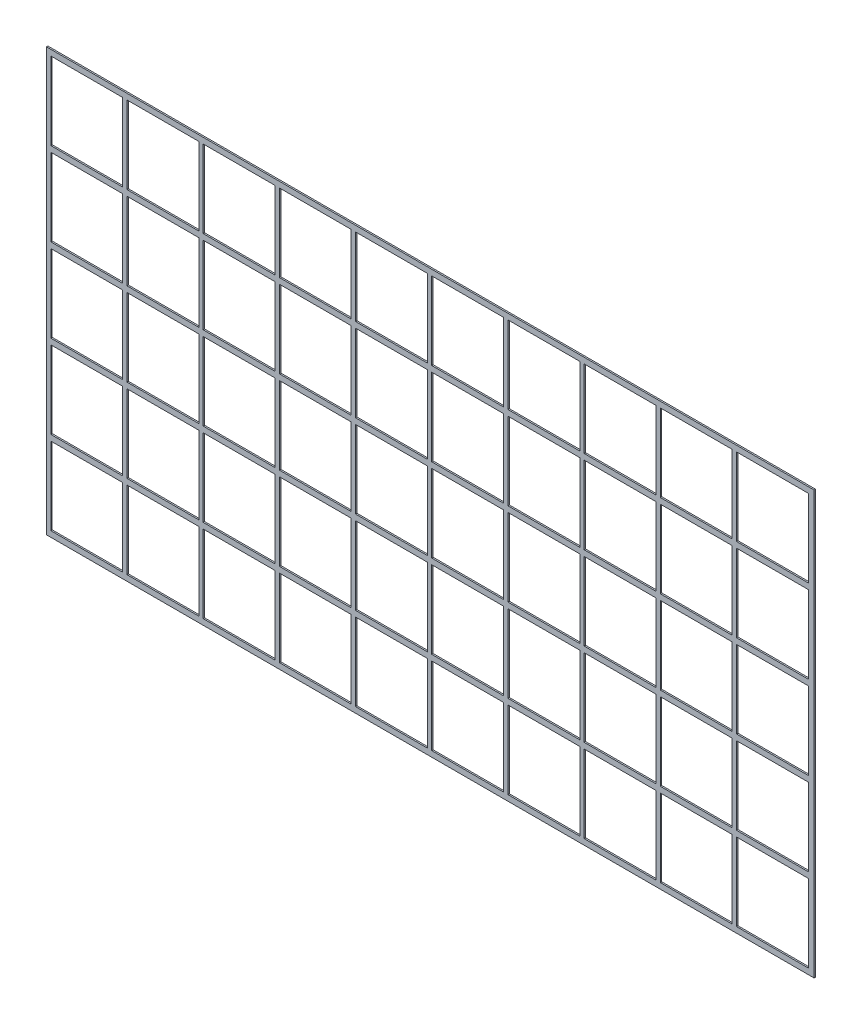
SolidWorks part; units mm, degrees
ref_plane "Front Plane" through (0, 0, 0) normal (0, 0, 1) x (1, 0, 0)
ref_plane "Top Plane" through (0, 0, 0) normal (0, 1, 0) x (1, 0, 0)
ref_plane "Right Plane" through (0, 0, 0) normal (1, 0, 0) x (0, 0, -1)
sketch "Sketch1" plane through (0, 0, 0) normal (0, 0, 1) x (1, 0, 0)
  line L1 (-847.725, -466.725) -> (847.725, -466.725)
  line L2 (-847.725, -466.725) -> (-847.725, 466.725)
  line L3 (-847.725, 466.725) -> (847.725, 466.725)
  line L4 (847.725, -466.725) -> (847.725, 466.725)
  line L5 (-847.725, -466.725) -> (847.725, 466.725) construction
  line L6 (-847.725, 466.725) -> (847.725, -466.725) construction
  point P0 (0, 0)
  dimension "D1" = 1695.45
  dimension "D2" = 933.45
extrude "Boss-Extrude1" add sketch "Sketch1" along normal blind 3.175
sketch "Sketch2" plane through (0, 0, 3.175) normal (0, 0, 1) x (1, 0, 0)
  line L1 (-679.45, 282.575) -> (-838.2, 282.575)
  line L2 (-679.45, 282.575) -> (-679.45, 454.025)
  line L3 (-679.45, 454.025) -> (-838.2, 454.025)
  line L4 (-838.2, 282.575) -> (-838.2, 454.025)
  line L5 (-679.45, 282.575) -> (-838.2, 454.025) construction
  line L6 (-679.45, 454.025) -> (-838.2, 282.575) construction
  line L8 (-511.175, 282.575) -> (-669.925, 282.575)
  line L9 (-511.175, 282.575) -> (-511.175, 454.025)
  line L10 (-511.175, 454.025) -> (-669.925, 454.025)
  line L11 (-669.925, 282.575) -> (-669.925, 454.025)
  line L12 (-342.9, 282.575) -> (-501.65, 282.575)
  line L13 (-342.9, 282.575) -> (-342.9, 454.025)
  line L14 (-342.9, 454.025) -> (-501.65, 454.025)
  line L15 (-501.65, 282.575) -> (-501.65, 454.025)
  line L16 (-174.625, 282.575) -> (-333.375, 282.575)
  line L17 (-174.625, 282.575) -> (-174.625, 454.025)
  line L18 (-174.625, 454.025) -> (-333.375, 454.025)
  line L19 (-333.375, 282.575) -> (-333.375, 454.025)
  line L20 (-6.35, 282.575) -> (-165.1, 282.575)
  line L21 (-6.35, 282.575) -> (-6.35, 454.025)
  line L22 (-6.35, 454.025) -> (-165.1, 454.025)
  line L23 (-165.1, 282.575) -> (-165.1, 454.025)
  line L24 (161.925, 282.575) -> (3.175, 282.575)
  line L25 (161.925, 282.575) -> (161.925, 454.025)
  line L26 (161.925, 454.025) -> (3.175, 454.025)
  line L27 (3.175, 282.575) -> (3.175, 454.025)
  line L28 (330.2, 282.575) -> (171.45, 282.575)
  line L29 (330.2, 282.575) -> (330.2, 454.025)
  line L30 (330.2, 454.025) -> (171.45, 454.025)
  line L31 (171.45, 282.575) -> (171.45, 454.025)
  line L32 (498.475, 282.575) -> (339.725, 282.575)
  line L33 (498.475, 282.575) -> (498.475, 454.025)
  line L34 (498.475, 454.025) -> (339.725, 454.025)
  line L35 (339.725, 282.575) -> (339.725, 454.025)
  line L36 (666.75, 282.575) -> (508, 282.575)
  line L37 (666.75, 282.575) -> (666.75, 454.025)
  line L38 (666.75, 454.025) -> (508, 454.025)
  line L39 (508, 282.575) -> (508, 454.025)
  line L40 (835.025, 282.575) -> (676.275, 282.575)
  line L41 (835.025, 282.575) -> (835.025, 454.025)
  line L42 (835.025, 454.025) -> (676.275, 454.025)
  line L43 (676.275, 282.575) -> (676.275, 454.025)
  line L44 (-511.175, 98.425) -> (-669.925, 98.425)
  line L45 (-511.175, 98.425) -> (-511.175, 269.875)
  line L46 (-511.175, 269.875) -> (-669.925, 269.875)
  line L47 (-669.925, 98.425) -> (-669.925, 269.875)
  line L48 (-342.9, 98.425) -> (-501.65, 98.425)
  line L49 (-342.9, 98.425) -> (-342.9, 269.875)
  line L50 (-342.9, 269.875) -> (-501.65, 269.875)
  line L51 (-501.65, 98.425) -> (-501.65, 269.875)
  line L52 (-174.625, 98.425) -> (-333.375, 98.425)
  line L53 (-174.625, 98.425) -> (-174.625, 269.875)
  line L54 (-174.625, 269.875) -> (-333.375, 269.875)
  line L55 (-333.375, 98.425) -> (-333.375, 269.875)
  line L56 (-6.35, 98.425) -> (-165.1, 98.425)
  line L57 (-6.35, 98.425) -> (-6.35, 269.875)
  line L58 (-6.35, 269.875) -> (-165.1, 269.875)
  line L59 (-165.1, 98.425) -> (-165.1, 269.875)
  line L60 (161.925, 98.425) -> (3.175, 98.425)
  line L61 (161.925, 98.425) -> (161.925, 269.875)
  line L62 (161.925, 269.875) -> (3.175, 269.875)
  line L63 (3.175, 98.425) -> (3.175, 269.875)
  line L64 (330.2, 98.425) -> (171.45, 98.425)
  line L65 (330.2, 98.425) -> (330.2, 269.875)
  line L66 (330.2, 269.875) -> (171.45, 269.875)
  line L67 (171.45, 98.425) -> (171.45, 269.875)
  line L68 (498.475, 98.425) -> (339.725, 98.425)
  line L69 (498.475, 98.425) -> (498.475, 269.875)
  line L70 (498.475, 269.875) -> (339.725, 269.875)
  line L71 (339.725, 98.425) -> (339.725, 269.875)
  line L72 (666.75, 98.425) -> (508, 98.425)
  line L73 (666.75, 98.425) -> (666.75, 269.875)
  line L74 (666.75, 269.875) -> (508, 269.875)
  line L75 (508, 98.425) -> (508, 269.875)
  line L76 (835.025, 98.425) -> (676.275, 98.425)
  line L77 (835.025, 98.425) -> (835.025, 269.875)
  line L78 (835.025, 269.875) -> (676.275, 269.875)
  line L79 (676.275, 98.425) -> (676.275, 269.875)
  line L80 (-511.175, -85.725) -> (-669.925, -85.725)
  line L81 (-511.175, -85.725) -> (-511.175, 85.725)
  line L82 (-511.175, 85.725) -> (-669.925, 85.725)
  line L83 (-669.925, -85.725) -> (-669.925, 85.725)
  line L84 (-342.9, -85.725) -> (-501.65, -85.725)
  line L85 (-342.9, -85.725) -> (-342.9, 85.725)
  line L86 (-342.9, 85.725) -> (-501.65, 85.725)
  line L87 (-501.65, -85.725) -> (-501.65, 85.725)
  line L88 (-174.625, -85.725) -> (-333.375, -85.725)
  line L89 (-174.625, -85.725) -> (-174.625, 85.725)
  line L90 (-174.625, 85.725) -> (-333.375, 85.725)
  line L91 (-333.375, -85.725) -> (-333.375, 85.725)
  line L92 (-6.35, -85.725) -> (-165.1, -85.725)
  line L93 (-6.35, -85.725) -> (-6.35, 85.725)
  line L94 (-6.35, 85.725) -> (-165.1, 85.725)
  line L95 (-165.1, -85.725) -> (-165.1, 85.725)
  line L96 (161.925, -85.725) -> (3.175, -85.725)
  line L97 (161.925, -85.725) -> (161.925, 85.725)
  line L98 (161.925, 85.725) -> (3.175, 85.725)
  line L99 (3.175, -85.725) -> (3.175, 85.725)
  line L100 (330.2, -85.725) -> (171.45, -85.725)
  line L101 (330.2, -85.725) -> (330.2, 85.725)
  line L102 (330.2, 85.725) -> (171.45, 85.725)
  line L103 (171.45, -85.725) -> (171.45, 85.725)
  line L104 (498.475, -85.725) -> (339.725, -85.725)
  line L105 (498.475, -85.725) -> (498.475, 85.725)
  line L106 (498.475, 85.725) -> (339.725, 85.725)
  line L107 (339.725, -85.725) -> (339.725, 85.725)
  line L108 (666.75, -85.725) -> (508, -85.725)
  line L109 (666.75, -85.725) -> (666.75, 85.725)
  line L110 (666.75, 85.725) -> (508, 85.725)
  line L111 (508, -85.725) -> (508, 85.725)
  line L112 (835.025, -85.725) -> (676.275, -85.725)
  line L113 (835.025, -85.725) -> (835.025, 85.725)
  line L114 (835.025, 85.725) -> (676.275, 85.725)
  line L115 (676.275, -85.725) -> (676.275, 85.725)
  line L116 (-511.175, -269.875) -> (-669.925, -269.875)
  line L117 (-511.175, -269.875) -> (-511.175, -98.425)
  line L118 (-511.175, -98.425) -> (-669.925, -98.425)
  line L119 (-669.925, -269.875) -> (-669.925, -98.425)
  line L120 (-342.9, -269.875) -> (-501.65, -269.875)
  line L121 (-342.9, -269.875) -> (-342.9, -98.425)
  line L122 (-342.9, -98.425) -> (-501.65, -98.425)
  line L123 (-501.65, -269.875) -> (-501.65, -98.425)
  line L124 (-174.625, -269.875) -> (-333.375, -269.875)
  line L125 (-174.625, -269.875) -> (-174.625, -98.425)
  line L126 (-174.625, -98.425) -> (-333.375, -98.425)
  line L127 (-333.375, -269.875) -> (-333.375, -98.425)
  line L128 (-6.35, -269.875) -> (-165.1, -269.875)
  line L129 (-6.35, -269.875) -> (-6.35, -98.425)
  line L130 (-6.35, -98.425) -> (-165.1, -98.425)
  line L131 (-165.1, -269.875) -> (-165.1, -98.425)
  line L132 (161.925, -269.875) -> (3.175, -269.875)
  line L133 (161.925, -269.875) -> (161.925, -98.425)
  line L134 (161.925, -98.425) -> (3.175, -98.425)
  line L135 (3.175, -269.875) -> (3.175, -98.425)
  line L136 (330.2, -269.875) -> (171.45, -269.875)
  line L137 (330.2, -269.875) -> (330.2, -98.425)
  line L138 (330.2, -98.425) -> (171.45, -98.425)
  line L139 (171.45, -269.875) -> (171.45, -98.425)
  line L140 (498.475, -269.875) -> (339.725, -269.875)
  line L141 (498.475, -269.875) -> (498.475, -98.425)
  line L142 (498.475, -98.425) -> (339.725, -98.425)
  line L143 (339.725, -269.875) -> (339.725, -98.425)
  line L144 (666.75, -269.875) -> (508, -269.875)
  line L145 (666.75, -269.875) -> (666.75, -98.425)
  line L146 (666.75, -98.425) -> (508, -98.425)
  line L147 (508, -269.875) -> (508, -98.425)
  line L148 (835.025, -269.875) -> (676.275, -269.875)
  line L149 (835.025, -269.875) -> (835.025, -98.425)
  line L150 (835.025, -98.425) -> (676.275, -98.425)
  line L151 (676.275, -269.875) -> (676.275, -98.425)
  line L152 (-511.175, -454.025) -> (-669.925, -454.025)
  line L153 (-511.175, -454.025) -> (-511.175, -282.575)
  line L154 (-511.175, -282.575) -> (-669.925, -282.575)
  line L155 (-669.925, -454.025) -> (-669.925, -282.575)
  line L156 (-342.9, -454.025) -> (-501.65, -454.025)
  line L157 (-342.9, -454.025) -> (-342.9, -282.575)
  line L158 (-342.9, -282.575) -> (-501.65, -282.575)
  line L159 (-501.65, -454.025) -> (-501.65, -282.575)
  line L160 (-174.625, -454.025) -> (-333.375, -454.025)
  line L161 (-174.625, -454.025) -> (-174.625, -282.575)
  line L162 (-174.625, -282.575) -> (-333.375, -282.575)
  line L163 (-333.375, -454.025) -> (-333.375, -282.575)
  line L164 (-6.35, -454.025) -> (-165.1, -454.025)
  line L165 (-6.35, -454.025) -> (-6.35, -282.575)
  line L166 (-6.35, -282.575) -> (-165.1, -282.575)
  line L167 (-165.1, -454.025) -> (-165.1, -282.575)
  line L168 (161.925, -454.025) -> (3.175, -454.025)
  line L169 (161.925, -454.025) -> (161.925, -282.575)
  line L170 (161.925, -282.575) -> (3.175, -282.575)
  line L171 (3.175, -454.025) -> (3.175, -282.575)
  line L172 (330.2, -454.025) -> (171.45, -454.025)
  line L173 (330.2, -454.025) -> (330.2, -282.575)
  line L174 (330.2, -282.575) -> (171.45, -282.575)
  line L175 (171.45, -454.025) -> (171.45, -282.575)
  line L176 (498.475, -454.025) -> (339.725, -454.025)
  line L177 (498.475, -454.025) -> (498.475, -282.575)
  line L178 (498.475, -282.575) -> (339.725, -282.575)
  line L179 (339.725, -454.025) -> (339.725, -282.575)
  line L180 (666.75, -454.025) -> (508, -454.025)
  line L181 (666.75, -454.025) -> (666.75, -282.575)
  line L182 (666.75, -282.575) -> (508, -282.575)
  line L183 (508, -454.025) -> (508, -282.575)
  line L184 (835.025, -454.025) -> (676.275, -454.025)
  line L185 (835.025, -454.025) -> (835.025, -282.575)
  line L186 (835.025, -282.575) -> (676.275, -282.575)
  line L187 (676.275, -454.025) -> (676.275, -282.575)
  line L188 (-679.45, 98.425) -> (-838.2, 98.425)
  line L189 (-679.45, 98.425) -> (-679.45, 269.875)
  line L190 (-679.45, 269.875) -> (-838.2, 269.875)
  line L191 (-838.2, 98.425) -> (-838.2, 269.875)
  line L192 (-679.45, -85.725) -> (-838.2, -85.725)
  line L193 (-679.45, -85.725) -> (-679.45, 85.725)
  line L194 (-679.45, 85.725) -> (-838.2, 85.725)
  line L195 (-838.2, -85.725) -> (-838.2, 85.725)
  line L196 (-679.45, -269.875) -> (-838.2, -269.875)
  line L197 (-679.45, -269.875) -> (-679.45, -98.425)
  line L198 (-679.45, -98.425) -> (-838.2, -98.425)
  line L199 (-838.2, -269.875) -> (-838.2, -98.425)
  line L200 (-679.45, -454.025) -> (-838.2, -454.025)
  line L201 (-679.45, -454.025) -> (-679.45, -282.575)
  line L202 (-679.45, -282.575) -> (-838.2, -282.575)
  line L203 (-838.2, -454.025) -> (-838.2, -282.575)
  line L204 (847.725, 466.725) -> (-847.725, 466.725) construction
  line L205 (-847.725, 466.725) -> (-847.725, -466.725) construction
  point P0 (-758.825, 368.3)
  dimension "D1" = 158.75
  dimension "D2" = 12.7
  dimension "D3" = 9.525
  dimension "D6" = 171.45
  dimension "D4" = 10
  dimension "D5" = 5
extrude "Cut-Extrude1" cut sketch "Sketch2" against normal through all
